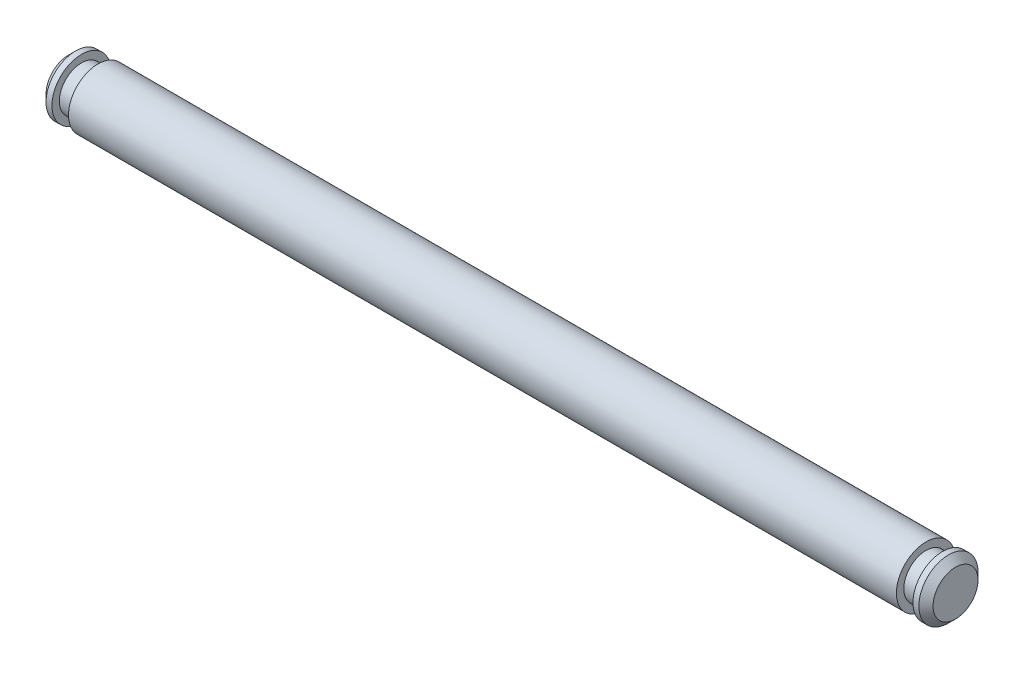
SolidWorks part; units mm, degrees
material "Plain Carbon Steel"
ref_plane "Front Plane" through (0, 0, 0) normal (0, 0, 1) x (1, 0, 0)
ref_plane "Top Plane" through (0, 0, 0) normal (0, 1, 0) x (1, 0, 0)
ref_plane "Right Plane" through (0, 0, 0) normal (1, 0, 0) x (0, 0, -1)
sketch "Sketch1" plane through (0, 0, 0) normal (0, 0, 1) x (1, 0, 0)
  line L0 (0, 0) -> (95.25, 0)
  line L1 (95.25, 0) -> (95.25, 2.413)
  line L2 (95.25, 2.413) -> (94.488, 3.175)
  line L3 (94.488, 3.175) -> (93.853, 3.175)
  line L4 (93.853, 3.175) -> (93.853, 2.3813)
  line L5 (93.853, 2.3813) -> (92.075, 2.3813)
  line L6 (92.075, 2.3813) -> (92.075, 3.175)
  line L7 (92.075, 3.175) -> (3.175, 3.175)
  line L8 (3.175, 3.175) -> (3.175, 2.3813)
  line L9 (3.175, 2.3813) -> (1.397, 2.3813)
  line L10 (1.397, 2.3813) -> (1.397, 3.175)
  line L11 (1.397, 3.175) -> (0.762, 3.175)
  line L12 (0.762, 3.175) -> (0, 2.413)
  line L13 (0, 2.413) -> (0, 0)
  line L14 (0, 0) -> (-4.8683, 0) construction
  dimension "D1" = 6.35
  dimension "D2" = 95.25
  dimension "D3" = 0.762
  dimension "D4" = 1.778
  dimension "D5" = 88.9
  dimension "D6" = 4.7625
revolve "Revolve1" add sketch "Sketch1" angle 360 about L14
